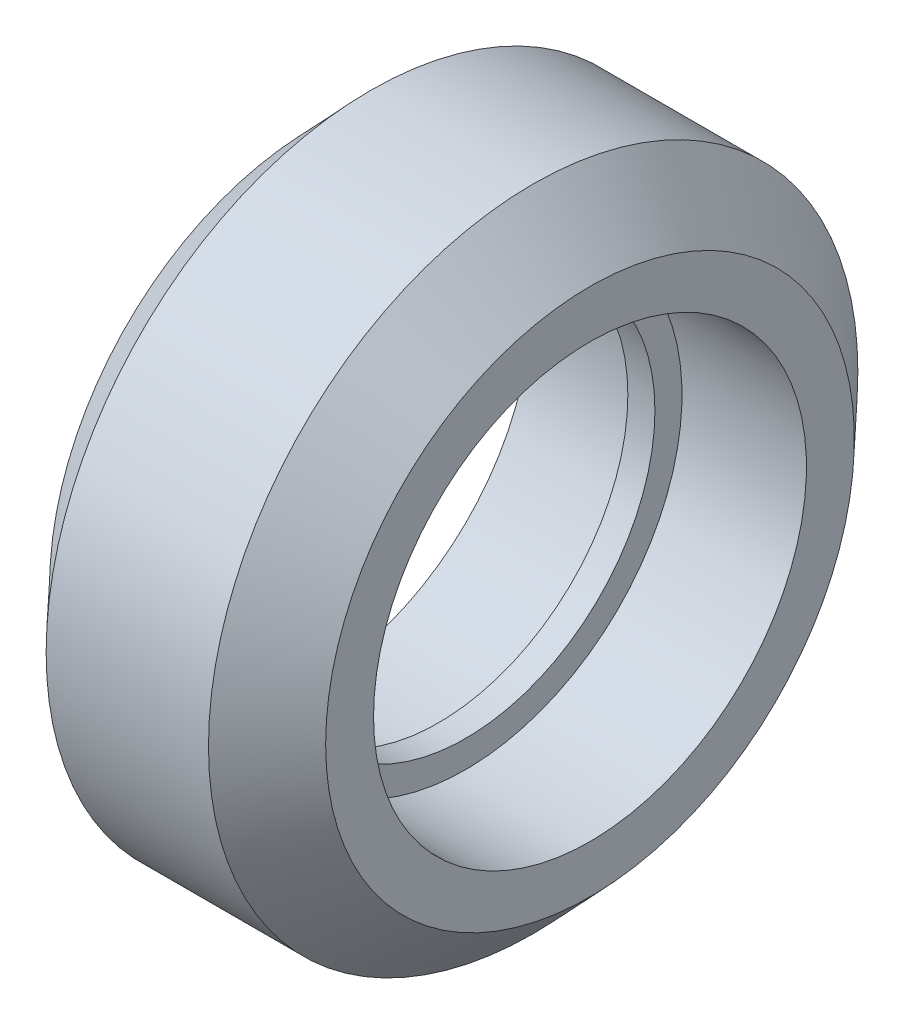
SolidWorks part; units mm, degrees
ref_plane "Front Plane" through (0, 0, 0) normal (0, 0, 1) x (1, 0, 0)
ref_plane "Top Plane" through (0, 0, 0) normal (0, 1, 0) x (1, 0, 0)
ref_plane "Right Plane" through (0, 0, 0) normal (1, 0, 0) x (0, 0, -1)
sketch "Sketch1" plane through (0, 0, 0) normal (0, 0, 1) x (1, 0, 0)
  line L0 (-3.4335, 0) -> (6.1117, 0) construction
  line L1 (0, 0) -> (0, 12) construction
  line L2 (-3, 12) -> (3, 12)
  line L3 (3, 12) -> (5.1, 9.77)
  line L4 (5.1, 9.77) -> (5.1, 8)
  line L5 (5.1, 8) -> (0.5, 8)
  line L6 (0.5, 8) -> (0.5, 7)
  line L7 (0.5, 7) -> (-0.5, 7)
  line L8 (-0.5, 8) -> (-0.5, 7)
  line L9 (-5.1, 8) -> (-0.5, 8)
  line L10 (-5.1, 9.77) -> (-5.1, 8)
  line L11 (-3, 12) -> (-5.1, 9.77)
  point P13 (0, 7)
  dimension "D1" = 5.1
  dimension "D2" = 3
  dimension "D3" = 12
  dimension "D4" = 7
  dimension "D5" = 0.5
  dimension "D6" = 9.77
  dimension "D7" = 8
revolve "Revolve1" add sketch "Sketch1" angle 360 about L0
